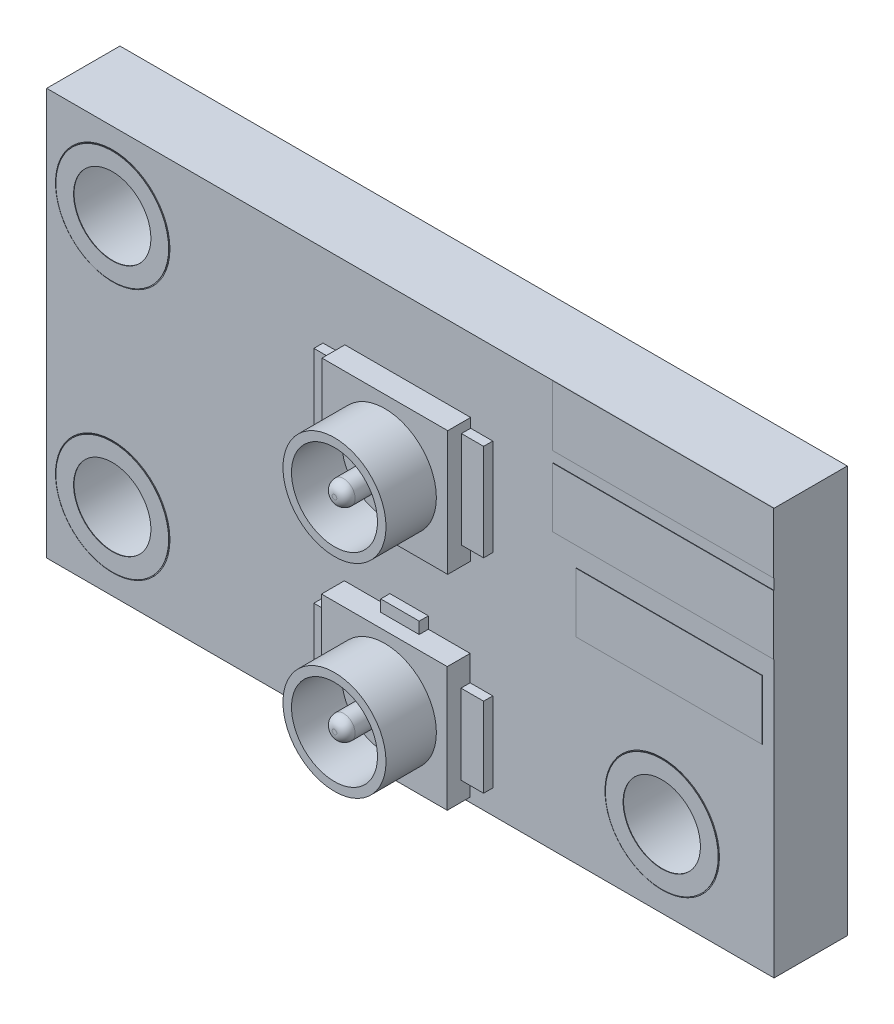
SolidWorks part; units mm, degrees
ref_plane "前视基准面" through (0, 0, 0) normal (0, 0, 1) x (1, 0, 0)
ref_plane "上视基准面" through (0, 0, 0) normal (0, 1, 0) x (1, 0, 0)
ref_plane "右视基准面" through (0, 0, 0) normal (1, 0, 0) x (0, 0, -1)
sketch "草图1" plane through (0, 0, 0) normal (0, 0, 1) x (1, 0, 0)
  line B0 (0, 11.811) -> (0, 0)
  circle B1 centre (3.336, 8.512) radius 1.65
  line B2 (10.5296, 10.1023) -> (1.8942, 10.1023)
  line B3 (1.9958, 10.2039) -> (1.9958, 1.3201)
  line B4 (7.2693, 6.149) -> (7.2693, 8.349)
  line B5 (8.279, 7.122) -> (7.4699, 7.122)
  line B6 (9.1872, 6.149) -> (9.1872, 7.3934)
  line B7 (12.7005, 5.5906) -> (10.16, 5.5906)
  circle B8 centre (15.336, 3.012) radius 1.9
  line B9 (12.1628, 1.4217) -> (17.7779, 1.4217)
  line B10 (17.7779, 1.3201) -> (12.1628, 1.3201)
  line B11 (17.6763, 1.3201) -> (17.6763, 5.363)
  arc B12 (8.829, 5.8925) -> (9.0856, 6.149) centre (8.829, 6.149) ccw
  line B13 (1.8942, 10.3055) -> (10.5296, 10.3055)
  line B14 (7.3709, 8.349) -> (7.3709, 6.149)
  line B15 (7.4725, 8.349) -> (7.4725, 6.149)
  arc B16 (7.2693, 8.349) -> (7.4725, 8.349) centre (7.3709, 8.349) ccw
  circle B17 centre (7.3709, 8.349) radius 0.1016
  arc B18 (9.1967, 5.0085) -> (8.7704, 4.5499) centre (9.2302, 4.5499) ccw
  arc B19 (9.2041, 4.9071) -> (8.872, 4.5499) centre (9.2302, 4.5499) ccw
  line B20 (10.3302, 3.0499) -> (10.3302, 4.5499)
  line B21 (10.729, 3.65) -> (10.729, 1.45)
  line B22 (17.526, 5.6177) -> (17.526, 6.9177)
  line B23 (13.315, 4.719) -> (13.9274, 5.3314)
  line B24 (17.526, 5.1579) -> (13.9992, 5.1579)
  line B25 (13.9992, 5.2595) -> (17.526, 5.2595)
  line B26 (19.558, 0) -> (19.558, 11.811)
  line B27 (17.526, 6.9177) -> (13.462, 6.9177)
  line B28 (17.526, 7.1742) -> (13.462, 7.1742)
  line B29 (12.954, 7.351) -> (18.034, 7.351)
  line B30 (12.1872, 6.149) -> (12.1872, 8.349)
  line B31 (10.729, 8.349) -> (10.729, 6.149)
  line B32 (1.8942, 10.2039) -> (10.5296, 10.2039)
  line B33 (19.558, 11.811) -> (0, 11.811)
  line B34 (8.152, 5.89) -> (8.152, 7.249)
  circle B35 centre (3.336, 3.012) radius 1.65
  line B36 (1.8942, 1.3201) -> (1.8942, 10.2039)
  line B37 (9.2302, 9.249) -> (9.2302, 7.749)
  line B38 (8.872, 9.249) -> (8.872, 8.7046)
  line B39 (8.406, 8.6081) -> (8.406, 7.249)
  arc B40 (8.829, 5.7909) -> (9.1872, 6.149) centre (8.829, 6.149) ccw
  arc B41 (8.829, 5.6893) -> (9.2888, 6.149) centre (8.829, 6.149) ccw
  line B42 (10.3302, 4.5499) -> (9.2302, 4.5499)
  arc B43 (9.6553, 5.5847) -> (9.799, 5.441) centre (9.7272, 5.5129) ccw
  line B44 (17.8795, 5.363) -> (17.8795, 1.3201)
  line B45 (1.8942, 1.4217) -> (7.3953, 1.4217)
  line B46 (0, 0) -> (19.558, 0)
  line B47 (9.1872, 1.45) -> (9.1872, 2.6944)
  line B48 (10.2693, 1.45) -> (10.2693, 2.6941)
  line B49 (10.4699, 2.677) -> (11.279, 2.677)
  line B50 (11.152, 2.55) -> (11.152, 3.9091)
  line B51 (11.829, 4.0082) -> (10.729, 4.0082)
  line B52 (12.954, 4.3663) -> (10.6883, 4.3663)
  line B53 (10.6883, 4.4679) -> (12.954, 4.4679)
  line B54 (13.462, 6.9177) -> (13.462, 5.6177)
  line B55 (11.829, 6.149) -> (11.829, 8.349)
  line B56 (10.3302, 7.2892) -> (9.2302, 7.2892)
  line B57 (7.729, 8.349) -> (7.729, 6.149)
  line B58 (9.2302, 7.749) -> (10.3302, 7.749)
  line B59 (12.2888, 8.349) -> (12.2888, 6.149)
  line B60 (11.152, 7.249) -> (11.152, 8.6081)
  line B61 (10.3302, 7.749) -> (10.3302, 9.249)
  line B62 (9.2302, 7.4924) -> (10.3302, 7.4924)
  line B63 (9.2302, 7.3908) -> (10.3302, 7.3908)
  line B64 (11.152, 5.89) -> (11.152, 7.249)
  line B65 (10.4725, 7.3931) -> (10.4725, 6.149)
  line B66 (8.829, 8.6056) -> (7.729, 8.6056)
  arc B67 (8.406, 8.6081) -> (8.152, 8.6081) centre (8.279, 8.6081) ccw
  line B68 (8.829, 8.7072) -> (7.729, 8.7072)
  line B69 (10.729, 6.149) -> (11.829, 6.149)
  line B70 (10.2693, 6.149) -> (10.2693, 7.3931)
  line B71 (8.829, 6.149) -> (8.829, 8.349)
  line B72 (8.829, 8.349) -> (7.729, 8.349)
  line B73 (7.729, 6.149) -> (8.829, 6.149)
  line B74 (7.729, 5.8925) -> (8.829, 5.8925)
  line B75 (7.729, 5.7909) -> (8.829, 5.7909)
  circle B76 centre (10.3302, 7.3908) radius 0.1016
  arc B77 (9.2302, 9.7087) -> (8.7704, 9.249) centre (9.2302, 9.249) ccw
  line B78 (12.954, 10.444) -> (12.954, 9.144)
  line B79 (11.3401, 9.1034) -> (12.5982, 9.1034)
  line B80 (10.9439, 8.8088) -> (11.829, 8.8088)
  line B81 (11.829, 8.7072) -> (10.9439, 8.7072)
  line B82 (11.829, 8.6056) -> (10.9439, 8.6056)
  line B83 (11.829, 8.349) -> (10.729, 8.349)
  line B84 (11.406, 8.6081) -> (11.406, 7.249)
  arc B85 (10.4699, 7.376) -> (10.4699, 7.122) centre (10.4699, 7.249) ccw
  line B86 (11.279, 7.122) -> (10.4699, 7.122)
  line B87 (11.406, 7.249) -> (11.406, 5.89)
  line B88 (8.279, 7.376) -> (9.0881, 7.376)
  line B89 (10.3709, 7.3931) -> (10.3709, 6.149)
  line B90 (10.4699, 7.376) -> (11.279, 7.376)
  line B91 (12.7005, 5.6922) -> (10.16, 5.6922)
  line B92 (10.729, 4.1098) -> (11.829, 4.1098)
  line B93 (11.829, 3.65) -> (10.729, 3.65)
  line B94 (9.2302, 2.6918) -> (10.3302, 2.6918)
  line B95 (9.2888, 2.6944) -> (9.2888, 1.45)
  line B96 (9.0856, 1.45) -> (9.0856, 2.6944)
  line B97 (8.829, 1.45) -> (8.829, 3.65)
  line B98 (9.0881, 2.423) -> (8.279, 2.423)
  line B99 (10.3302, 2.5902) -> (9.2302, 2.5902)
  line B100 (9.2302, 2.7934) -> (10.3302, 2.7934)
  line B101 (9.2302, 3.0499) -> (10.3302, 3.0499)
  line B102 (9.2302, 4.5499) -> (9.2302, 3.0499)
  line B103 (8.829, 3.65) -> (7.729, 3.65)
  line B104 (10.729, 5.7909) -> (11.829, 5.7909)
  line B105 (10.729, 5.8925) -> (11.829, 5.8925)
  line B106 (10.6883, 4.5695) -> (12.954, 4.5695)
  line B107 (11.406, 3.9091) -> (11.406, 2.55)
  line B108 (11.279, 2.677) -> (12.0881, 2.677)
  line B109 (11.829, 1.45) -> (11.829, 3.65)
  line B110 (12.0881, 2.423) -> (11.279, 2.423)
  line B111 (11.279, 2.423) -> (10.4699, 2.423)
  line B112 (8.406, 3.9091) -> (8.406, 2.55)
  line B113 (10.4725, 2.6941) -> (10.4725, 1.45)
  line B114 (10.729, 1.45) -> (11.829, 1.45)
  line B115 (8.152, 7.249) -> (8.152, 8.6081)
  line B116 (9.2888, 7.3934) -> (9.2888, 6.149)
  line B117 (10.6883, 4.0059) -> (10.6883, 4.4679)
  line B118 (9.799, 5.441) -> (9.4192, 5.0612)
  line B119 (7.2693, 1.45) -> (7.2693, 3.65)
  line B120 (7.4699, 2.677) -> (8.279, 2.677)
  line B121 (10.3302, 4.5499) -> (9.2302, 4.5499)
  line B122 (7.729, 4.1098) -> (8.829, 4.1098)
  line B123 (17.7779, 1.2185) -> (12.1628, 1.2185)
  arc B124 (12.954, 4.3663) -> (13.4587, 4.5753) centre (12.954, 5.08) ccw
  line B125 (12.6286, 5.764) -> (13.032, 6.1674)
  line B126 (13.9992, 5.3611) -> (17.526, 5.3611)
  line B127 (13.462, 5.6177) -> (17.526, 5.6177)
  arc B128 (10.3824, 7.2922) -> (10.3593, 7.4941) centre (10.3709, 7.3931) ccw
  arc B129 (10.3709, 6.149) -> (10.729, 5.7909) centre (10.729, 6.149) ccw
  line B130 (18.034, 7.351) -> (18.034, 8.651)
  line B131 (17.6763, 7.1723) -> (17.6763, 8.7859)
  line B132 (12.0856, 6.149) -> (12.0856, 8.349)
  line B133 (17.7779, 5.363) -> (17.7779, 1.3201)
  line B134 (13.1757, 6.0237) -> (12.7723, 5.6203)
  line B135 (13.1039, 6.0956) -> (12.7005, 5.6922)
  line B136 (17.8795, 8.7859) -> (17.8795, 7.1723)
  line B137 (17.7779, 8.7859) -> (17.7779, 7.1723)
  line B138 (18.034, 8.651) -> (12.954, 8.651)
  line B139 (12.954, 9.144) -> (18.034, 9.144)
  line B140 (12.954, 8.8875) -> (17.7779, 8.8875)
  line B141 (12.954, 8.7859) -> (17.7779, 8.7859)
  line B142 (17.7779, 8.6843) -> (12.954, 8.6843)
  line B143 (13.462, 7.3774) -> (17.526, 7.3774)
  arc B144 (17.8494, 7.2445) -> (17.526, 7.3774) centre (17.526, 6.9177) ccw
  arc B145 (17.7779, 7.1723) -> (17.526, 7.2758) centre (17.526, 6.9177) ccw
sketch_block_instance "DXF_Sample_ConnectBoard_2023-05-06-1"
sketch_block "DXF_Sample_ConnectBoard_2023-05-06"
sketch "草图2" plane through (0, 0, 0) normal (0, 0, 1) x (1, 0, 0)
  line L1 (1.8942, 10.2039) -> (17.7779, 10.2039)
  line L2 (1.8942, 10.2039) -> (1.8942, 1.3201)
  line L3 (1.8942, 1.3201) -> (17.7779, 1.3201)
  line L4 (17.7779, 10.2039) -> (17.7779, 1.3201)
extrude "凸台-拉伸1" add sketch "草图2" along normal blind 1.6
sketch "草图3" plane through (0, 0, 1.6) normal (0, 0, 1) x (1, 0, 0)
  circle A0 centre (3.336, 8.512) radius 1.25
  circle A1 centre (15.336, 3.012) radius 1.25
  circle A2 centre (3.336, 3.012) radius 1.25
  dimension "D1" = 2.5
extrude "切除-拉伸1" cut sketch "草图3" against normal through all
sketch "草图4" plane through (0, 0, 1.6) normal (0, 0, 1) x (1, 0, 0)
  line L0 (8.3953, 1.4226) -> (11.1413, 1.4226)
  line L1 (8.406, 5.89) -> (11.152, 5.89)
  line L2 (8.406, 5.89) -> (8.406, 8.6081)
  line L3 (8.406, 8.6081) -> (11.152, 8.6081)
  line L4 (11.152, 5.89) -> (11.152, 8.6081)
  line L5 (8.3953, 1.4226) -> (8.3953, 4.1408)
  line L6 (8.3953, 4.1408) -> (11.1413, 4.1408)
  line L7 (11.1413, 1.4226) -> (11.1413, 4.1408)
extrude "凸台-拉伸2" add sketch "草图4" along normal blind 0.5
sketch "草图5" plane through (0, 0, 2.1) normal (0, 0, 1) x (1, 0, 0)
  circle A0 centre (9.779, 7.215) radius 1.125
  circle A1 centre (9.779, 2.7735) radius 1.125
extrude "凸台-拉伸3" add sketch "草图5" along normal blind 1.1
sketch "草图6" plane through (0, 0, 3.2) normal (0, 0, 1) x (1, 0, 0)
  circle A0 centre (9.779, 7.215) radius 0.9391
  circle A1 centre (9.779, 2.7735) radius 0.9391
  circle A2 centre (9.779, 7.215) radius 0.2507
  circle A3 centre (9.779, 2.7735) radius 0.2507
extrude "切除-拉伸2" cut sketch "草图6" against normal blind 1.1
sketch "草图7" plane through (0, 0, 1.6) normal (0, 0, 1) x (1, 0, 0)
  line L0 (12.954, 10.444) -> (12.954, 9.144) construction
  line L1 (12.954, 10.2111) -> (17.7779, 10.2111)
  line L2 (12.954, 10.2111) -> (12.954, 8.8875)
  line L3 (12.954, 8.8875) -> (17.7779, 8.8875)
  line L4 (17.7779, 10.2111) -> (17.7779, 8.8875)
  line L5 (12.954, 7.351) -> (18.034, 7.351) construction
  line L6 (12.954, 8.651) -> (17.7779, 8.651)
  line L7 (12.954, 8.651) -> (12.954, 7.351)
  line L8 (12.954, 7.351) -> (17.7779, 7.351)
  line L9 (17.7779, 8.651) -> (17.7779, 7.351)
  line L11 (13.462, 6.9177) -> (17.526, 6.9177)
  line L12 (13.462, 6.9177) -> (13.462, 5.6177)
  line L13 (13.462, 5.6177) -> (17.526, 5.6177)
  line L14 (17.526, 6.9177) -> (17.526, 5.6177)
extrude "凸台-拉伸4" add sketch "草图7" along normal blind 0.01
sketch "草图8" plane through (0, 0, 1.6) normal (0, 0, 1) x (1, 0, 0)
  circle A0 centre (3.336, 8.512) radius 1.2314
  circle A1 centre (3.336, 3.012) radius 1.2314
  circle A2 centre (15.336, 3.012) radius 1.2314
  circle A3 centre (3.336, 8.512) radius 0.8443
  circle A4 centre (3.336, 3.012) radius 0.8443
  circle A5 centre (15.336, 3.012) radius 0.8443
extrude "凸台-拉伸5" add sketch "草图8" along normal blind 0.01 separate body
ref_plane "基准面1" through (17.7779, 1.3201, 0) normal (1, 0, 0) x (0, 0, -1)
sketch "草图10" plane through (0, 0, 1.6) normal (0, 0, 1) x (1, 0, 0)
  line L0 (8.406, 8.6081) -> (8.406, 5.89) construction
  line L1 (8.406, 8.4034) -> (7.9289, 8.4034)
  line L2 (8.406, 8.4034) -> (8.406, 6.2942)
  line L3 (8.406, 6.2942) -> (7.9289, 6.2942)
  line L4 (7.9289, 8.4034) -> (7.9289, 6.2942)
  line L5 (11.152, 5.89) -> (11.152, 8.6081) construction
  line L6 (11.152, 6.2942) -> (11.6353, 6.2942)
  line L7 (11.152, 6.2942) -> (11.152, 8.4034)
  line L8 (11.152, 8.4034) -> (11.6353, 8.4034)
  line L9 (11.6353, 6.2942) -> (11.6353, 8.4034)
  line L10 (8.406, 5.89) -> (11.152, 5.89) construction
  line L11 (9.3885, 5.89) -> (10.2292, 5.89)
  line L12 (9.3885, 5.89) -> (9.3885, 5.6294)
  line L13 (9.3885, 5.6294) -> (10.2292, 5.6294)
  line L14 (10.2292, 5.89) -> (10.2292, 5.6294)
  line L15 (8.3953, 4.1408) -> (8.3953, 1.4226) construction
  line L16 (8.3953, 3.5841) -> (7.9289, 3.5841)
  line L17 (8.3953, 3.5841) -> (8.3953, 1.8424)
  line L18 (8.3953, 1.8424) -> (7.9289, 1.8424)
  line L19 (7.9289, 3.5841) -> (7.9289, 1.8424)
  line L20 (11.1413, 1.4226) -> (11.1413, 4.1408) construction
  line L21 (11.1413, 1.8424) -> (11.6353, 1.8424)
  line L22 (11.1413, 1.8424) -> (11.1413, 3.5841)
  line L23 (11.1413, 3.5841) -> (11.6353, 3.5841)
  line L24 (11.6353, 1.8424) -> (11.6353, 3.5841)
  line L25 (11.1413, 4.1408) -> (8.3953, 4.1408) construction
  line L26 (9.3885, 4.1408) -> (10.2292, 4.1408)
  line L27 (9.3885, 4.1408) -> (9.3885, 4.3951)
  line L28 (9.3885, 4.3951) -> (10.2292, 4.3951)
  line L29 (10.2292, 4.1408) -> (10.2292, 4.3951)
extrude "凸台-拉伸6" add sketch "草图10" along normal blind 0.2
fillet "圆角1" radius 0.2 2 edges at (10.0298, 2.7735, 3.2) (10.0298, 7.215, 3.2)
